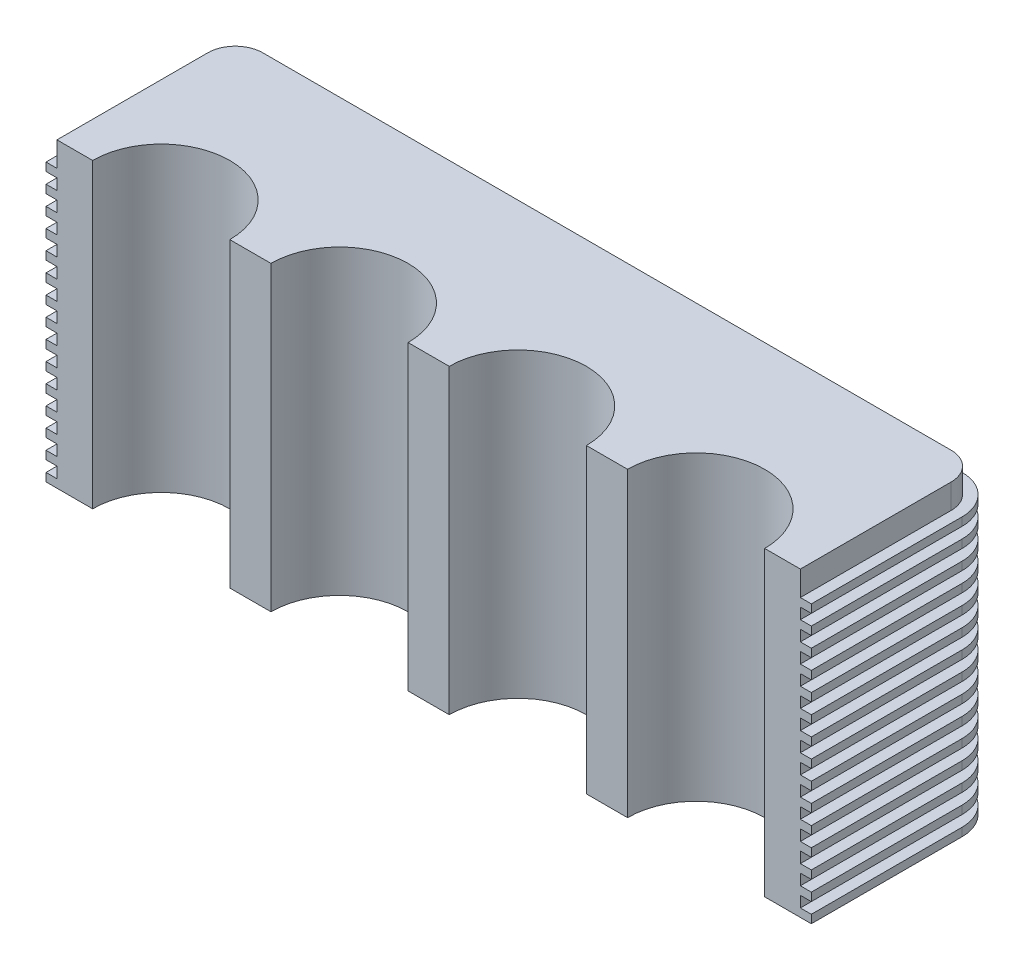
SolidWorks part; units mm, degrees
ref_plane "Front Plane" through (0, 0, 0) normal (0, 0, 1) x (1, 0, 0)
ref_plane "Top Plane" through (0, 0, 0) normal (0, 1, 0) x (1, 0, 0)
ref_plane "Right Plane" through (0, 0, 0) normal (1, 0, 0) x (0, 0, -1)
sketch "Sketch1" plane through (0, 0, 0) normal (0, 1, 0) x (1, 0, 0)
  line L0 (135.5, 65) -> (135.5, 0) construction
  line L1 (0, 0) -> (13, 0)
  line L2 (0, 0) -> (0, 55)
  line L3 (10, 65) -> (261, 65)
  line L4 (271, 0) -> (271, 55)
  line L5 (258, 0) -> (271, 0)
  line L6 (193, 0) -> (208, 0)
  line L7 (63, 0) -> (78, 0)
  line L8 (128, 0) -> (143, 0)
  arc A0 (261, 65) -> (271, 55) centre (261, 55) cw
  arc A1 (0, 55) -> (10, 65) centre (10, 55) cw
  arc A2 (258, 0) -> (208, 0) centre (233, 0) ccw
  arc A3 (193, 0) -> (143, 0) centre (168, 0) ccw
  arc A4 (13, 0) -> (63, 0) centre (38, 0) cw
  arc A5 (78, 0) -> (128, 0) centre (103, 0) cw
  dimension "D1" = 10
  dimension "D4" = 25
  dimension "D6" = 50
  dimension "D2" = 271
  dimension "D3" = 65
  dimension "D5" = 13
  dimension "D7" = 15
extrude "Boss-Extrude1" add sketch "Sketch1" along normal blind 110
sketch "Sketch4" plane through (0, 0, 0) normal (0, 1, 0) x (1, 0, 0)
  line L0 (275, 0) -> (275, 55)
  line L1 (261, 69) -> (10, 69)
  line L2 (-4, 55) -> (-4, 0)
  line L3 (271, 0) -> (275, 0)
  line L4 (0, 0) -> (-4, 0)
  line L8 (0, 55) -> (0, 0)
  line L9 (261, 65) -> (10, 65)
  line L10 (271, 0) -> (271, 55)
  line L11 (258, 0) -> (271, 0)
  line L12 (193, 0) -> (208, 0)
  line L13 (128, 0) -> (143, 0)
  line L14 (63, 0) -> (78, 0)
  line L15 (0, 0) -> (13, 0)
  line L16 (0, 55) -> (0, 0)
  line L17 (261, 65) -> (10, 65)
  line L18 (271, 0) -> (271, 55)
  arc A0 (275, 55) -> (261, 69) centre (261, 55) ccw
  arc A1 (10, 69) -> (-4, 55) centre (10, 55) ccw
  arc A6 (10, 65) -> (0, 55) centre (10, 55) ccw
  arc A7 (271, 55) -> (261, 65) centre (261, 55) ccw
  arc A8 (258, 0) -> (208, 0) centre (233, 0) ccw
  arc A9 (193, 0) -> (143, 0) centre (168, 0) ccw
  arc A10 (128, 0) -> (78, 0) centre (103, 0) ccw
  arc A11 (63, 0) -> (13, 0) centre (38, 0) ccw
  arc A12 (10, 65) -> (0, 55) centre (10, 55) ccw
  arc A13 (271, 55) -> (261, 65) centre (261, 55) ccw
  dimension "D1" = 0
  dimension "D2" = 4
extrude "Boss-Extrude2" add sketch "Sketch4" along normal blind 3
pattern_linear "LPattern1" count 15 spacing 7 along (0, 1, 0) of "Boss-Extrude2"
